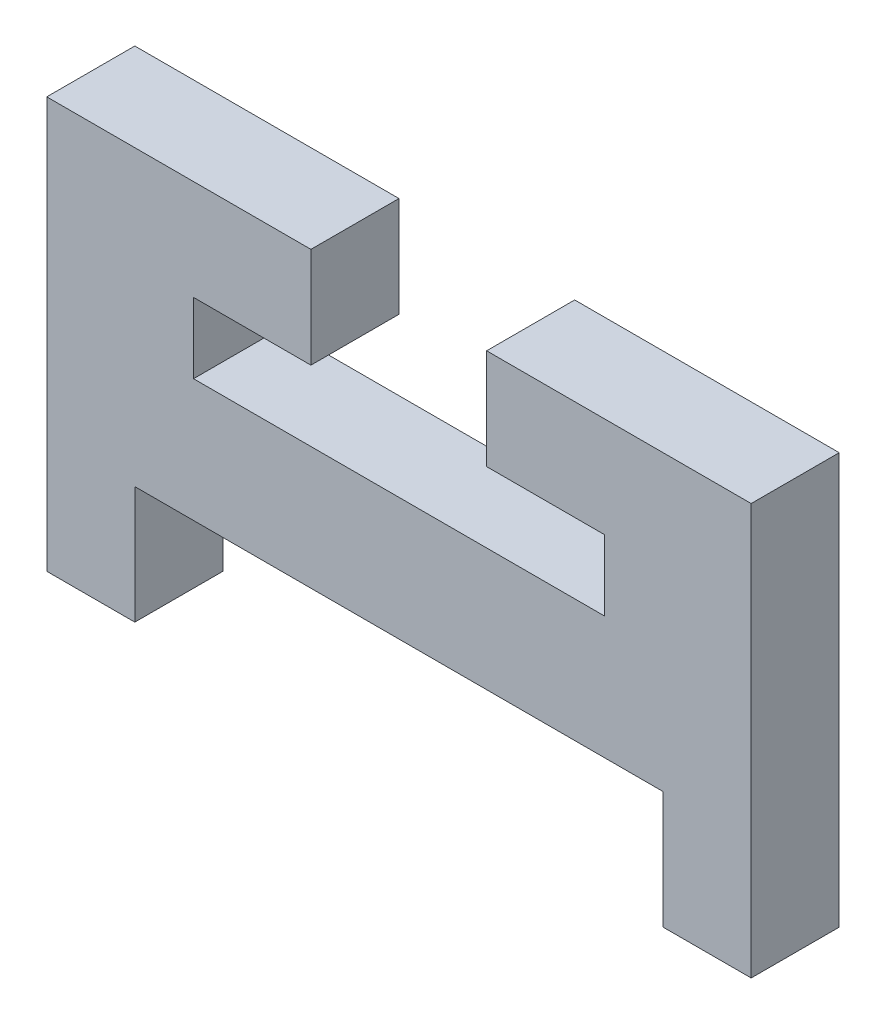
SolidWorks part; units mm, degrees
ref_plane "Alzado" through (0, 0, 0) normal (0, 0, 1) x (1, 0, 0)
ref_plane "Planta" through (0, 0, 0) normal (0, 1, 0) x (1, 0, 0)
ref_plane "Vista lateral" through (0, 0, 0) normal (1, 0, 0) x (0, 0, -1)
sketch "Model" plane through (0, 0, 0) normal (0, 0, 1) x (1, 0, 0)
  line L0 (33.6, 16.0827) -> (26.1, 16.0827)
  line L1 (26.1, 16.0827) -> (26.1, 18.4827)
  line L2 (26.1, 18.4827) -> (30.1, 18.4827)
  line L3 (30.1, 18.4827) -> (30.1, 21.9)
  line L4 (30.1, 21.9) -> (21.1, 21.9)
  line L5 (21.1, 21.9) -> (21.1, 7.9)
  line L6 (21.1, 7.9) -> (24.1, 7.9)
  line L7 (24.1, 7.9) -> (24.1, 11.9)
  line L8 (24.1, 11.9) -> (42.1, 11.9)
  line L9 (42.1, 11.9) -> (42.1, 7.9)
  line L10 (42.1, 7.9) -> (45.1, 7.9)
  line L11 (45.1, 7.9) -> (45.1, 21.9)
  line L12 (45.1, 21.9) -> (36.0864, 21.9)
  line L13 (36.0864, 21.9) -> (36.0864, 18.4827)
  line L14 (36.0864, 18.4827) -> (40.1, 18.4827)
  line L15 (40.1, 18.4827) -> (40.1, 16.0827)
  line L16 (40.1, 16.0827) -> (33.6, 16.0827)
extrude "Saliente-Extruir1" add sketch "Model" along normal blind 3
